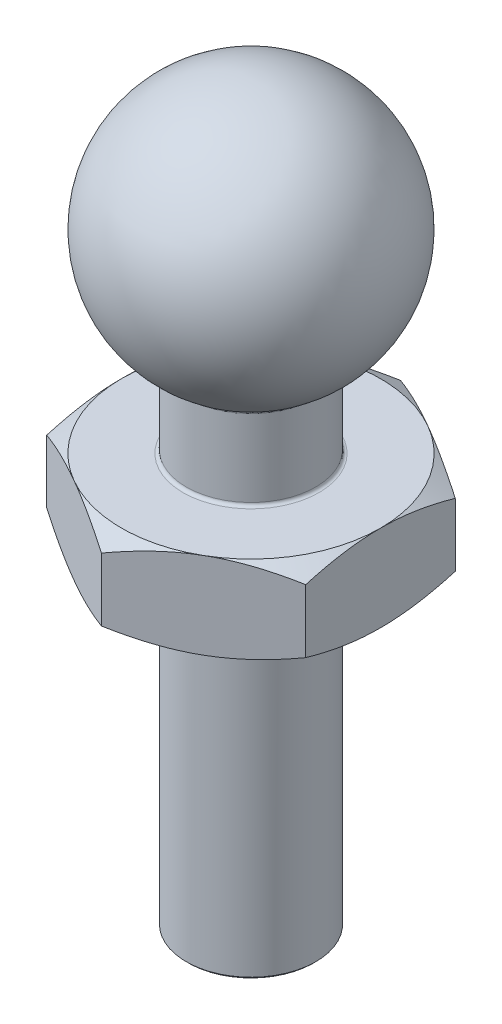
SolidWorks part; units mm, degrees
ref_plane "Front Plane" through (0, 0, 0) normal (0, 0, 1) x (1, 0, 0)
ref_plane "Top Plane" through (0, 0, 0) normal (0, 1, 0) x (1, 0, 0)
ref_plane "Right Plane" through (0, 0, 0) normal (1, 0, 0) x (0, 0, -1)
sketch "Sketch1" plane through (0, 0, 0) normal (0, 0, 1) x (1, 0, 0)
  line L1 (0, 0) -> (1.5, 0)
  line L2 (1.5, 0) -> (1.5, 11.4019)
  line L3 (0, 0) -> (0, 11)
  line L4 (0, 11) -> (0, 17)
  circle A0 centre (0, 14) radius 3 construction
  arc A1 (0, 17) -> (1.5, 11.4019) centre (0, 14) cw
  dimension "D1" = 6
  dimension "D2" = 1.5
  dimension "D3" = 11
revolve "Revolve1" add sketch "Sketch1" angle 360 about L3
sketch "Sketch2" plane through (0, 0, 0) normal (0, 0, 1) x (1, 0, 0)
  line L0 (-3.4002, 7.5) -> (3.4002, 7.5)
  point P2 (0, 7.5)
  dimension "D1" = 7.5
split line "Split Line1"
chamfer "Chamfer1" distance 0.05 angle 45 1 edges at (0, 0, -1.5)
ref_plane "Plane1" through (0, 7.5, 0) normal (0, 1, 0) x (1, 0, 0)
sketch "Sketch4" plane through (0, 7.5, 0) normal (0, 1, 0) x (1, 0, 0)
  line L1 (3, -1.7321) -> (3, 1.7321)
  line L2 (3, 1.7321) -> (0, 3.4641)
  line L3 (0, 3.4641) -> (-3, 1.7321)
  line L4 (-3, 1.7321) -> (-3, -1.7321)
  line L5 (-3, -1.7321) -> (0, -3.4641)
  line L6 (0, -3.4641) -> (3, -1.7321)
  circle A0 centre (0, 0) radius 1.5 construction
  circle A1 centre (0, 0) radius 3 construction
  circle A2 centre (0, 0) radius 1.5 construction
  dimension "D1" = 6
extrude "Boss-Extrude1" add sketch "Sketch4" along normal blind 2
sketch "Sketch5" plane through (0, 7.5, 0) normal (0, -1, 0) x (1, 0, 0)
sketch "Sketch6" plane through (0, 7.5, 0) normal (0, -1, 0) x (1, 0, 0)
  circle A0 centre (0, 0) radius 3 construction
  circle A1 centre (0, 0) radius 3
extrude "Cut-Extrude1" cut sketch "Sketch6" against normal blind 2 draft 60 flip side to cut
sketch "Sketch7" plane through (0, 9.5, 0) normal (0, 1, 0) x (1, 0, 0)
  circle A0 centre (0, 0) radius 3 construction
  circle A1 centre (0, 0) radius 3
extrude "Cut-Extrude2" cut sketch "Sketch7" against normal blind 2 draft 60 flip side to cut
fillet "Fillet1" radius 0.075 2 edges at (0, 11.4019, -1.5) (0, 9.5, 1.5)
